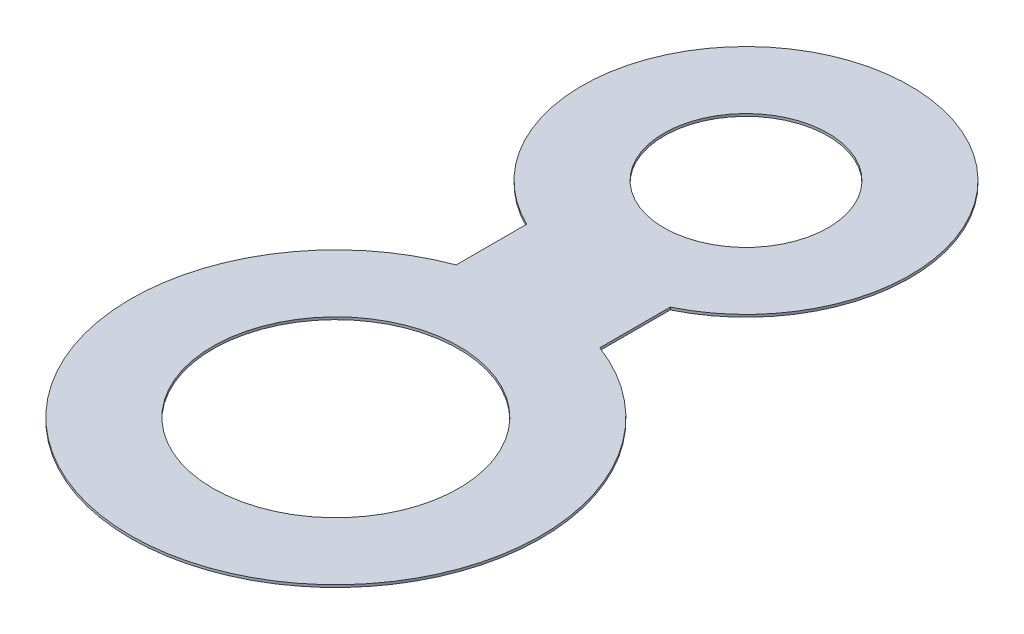
SolidWorks part; units mm, degrees
ref_plane "Front Plane" through (0, 0, 0) normal (0, 0, 1) x (1, 0, 0)
ref_plane "Top Plane" through (0, 0, 0) normal (0, 1, 0) x (1, 0, 0)
ref_plane "Right Plane" through (0, 0, 0) normal (1, 0, 0) x (0, 0, -1)
sketch "Sketch1" plane through (0, 0, 0) normal (0, 1, 0) x (1, 0, 0)
  line L1 (0, -55) -> (0, 55) construction
  line L6 (-8.75, 40) -> (8.75, 40)
  line L7 (-8.75, 40) -> (-8.75, 15)
  line L8 (-8.75, 15) -> (8.75, 15)
  line L9 (8.75, 40) -> (8.75, 15)
  line L10 (-8.75, 40) -> (8.75, 15) construction
  line L11 (-8.75, 15) -> (8.75, 40) construction
  circle A0 centre (0, 0) radius 15
  circle A1 centre (0, 50) radius 10
  circle A2 centre (0, 50) radius 20
  circle A3 centre (0, 0) radius 25
  point P11 (0, 27.5)
  point P15 (0, 39)
  dimension "D5" = 20
  dimension "D6" = 30
  dimension "D1" = 0
  dimension "D2" = 0
  dimension "D3" = 50
  dimension "D8" = 0
  dimension "D12" = 0
  dimension "D10" = 0
  dimension "D9" = 15
  dimension "D11" = 10
  dimension "D13" = 17.5
  dimension "D4" = 10
  dimension "D7" = 10
extrude "Boss-Extrude1" add sketch "Sketch1" along normal blind 0.3
equation "\"D9@Sketch1\"=\"D6@Sketch1\"/2"
equation "\"D11@Sketch1\"=\"D5@Sketch1\"/2"
